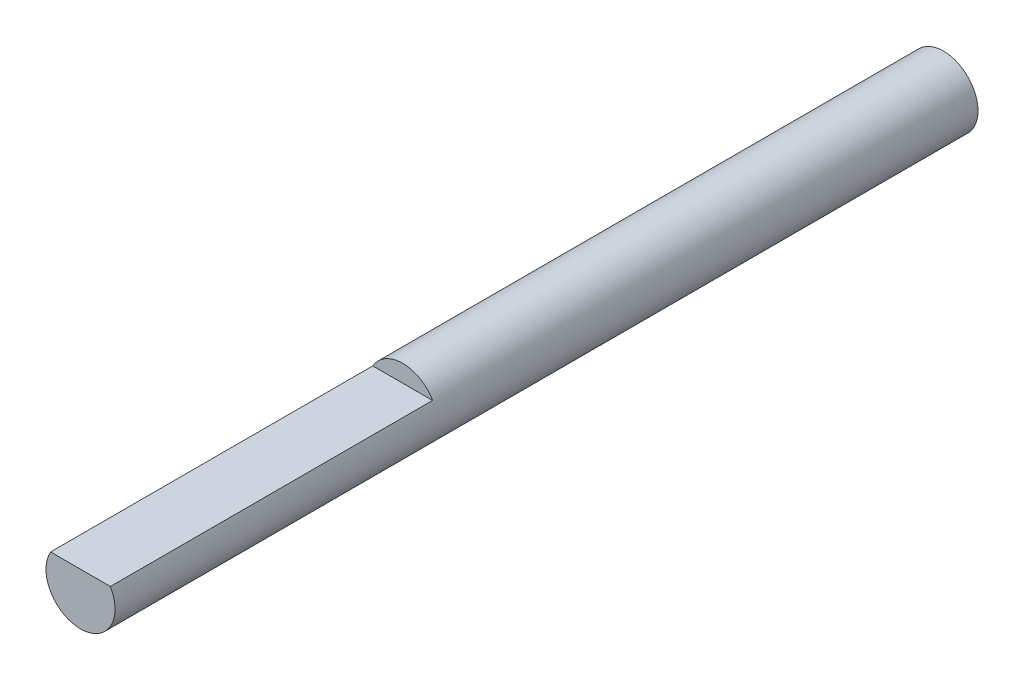
SolidWorks part; units mm, degrees
material "1060 Alloy"
ref_plane "Front Plane" through (0, 0, 0) normal (0, 0, 1) x (1, 0, 0)
ref_plane "Top Plane" through (0, 0, 0) normal (0, 1, 0) x (1, 0, 0)
ref_plane "Right Plane" through (0, 0, 0) normal (1, 0, 0) x (0, 0, -1)
sketch "Sketch2" plane through (0, 0, 0) normal (0, 0, 1) x (1, 0, 0)
  circle A0 centre (0, 0) radius 6
  dimension "D1" = 12
extrude "Boss-Extrude1" add sketch "Sketch2" along normal blind 150
sketch "Sketch3" plane through (0, 0, 150) normal (0, 0, 1) x (1, 0, 0)
  line L0 (-5.1962, 3) -> (5.1962, 3)
  circle A0 centre (0, 0) radius 6 construction
  arc A1 (-5.1962, 3) -> (5.1962, 3) centre (0, 0) ccw
  arc A2 (-5.1962, 3) -> (5.1962, 3) centre (0, 0) cw
  point P5 (0, 6)
  circle M3 centre (0, 0) radius 6
  dimension "D1" = 3
extrude "Cut-Extrude1" cut sketch "Sketch3" against normal blind 56 contours L0 M3
